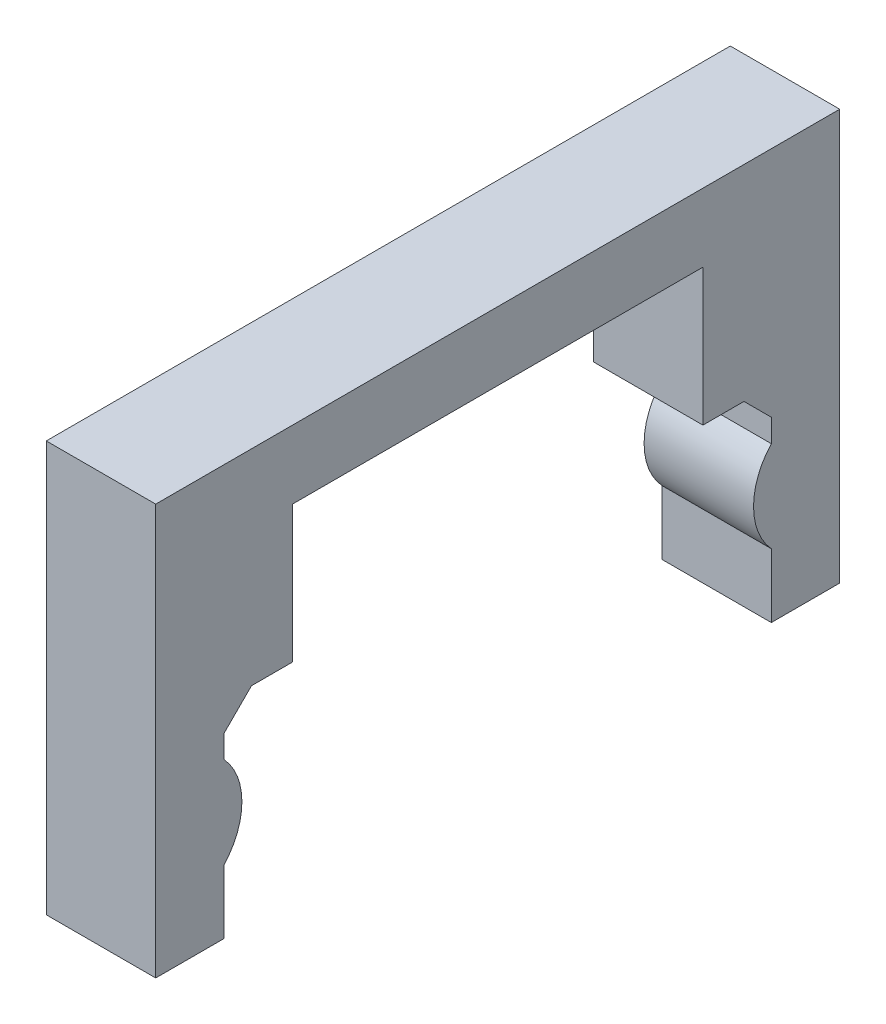
SolidWorks part; units mm, degrees
ref_plane "Front Plane" through (0, 0, 0) normal (0, 0, 1) x (1, 0, 0)
ref_plane "Top Plane" through (0, 0, 0) normal (0, 1, 0) x (1, 0, 0)
ref_plane "Right Plane" through (0, 0, 0) normal (1, 0, 0) x (0, 0, -1)
sketch "Sketch3" plane through (0, 0, 0) normal (1, 0, 0) x (0, 0, -1)
  line L0 (-101.8456, -9.1027) -> (-95.4956, -9.1027)
  line L1 (-95.4956, -9.1027) -> (-95.4956, 9.9473)
  line L2 (-95.4956, 9.9473) -> (-89.1456, 9.9473)
  line L3 (-89.1456, 9.9473) -> (-89.1456, 22.6473)
  line L4 (-89.1456, 22.6473) -> (-51.0456, 22.6473)
  line L5 (-51.0456, 22.6473) -> (-51.0456, 9.9473)
  line L6 (-51.0456, 9.9473) -> (-44.6956, 9.9473)
  line L7 (-44.6956, 9.9473) -> (-44.6956, -9.1027)
  line L8 (-44.6956, -9.1027) -> (-38.3456, -9.1027)
  line L9 (-38.3456, -9.1027) -> (-38.3456, 28.9973)
  line L10 (-38.3456, 28.9973) -> (-101.8456, 28.9973)
  line L11 (-101.8456, 28.9973) -> (-101.8456, -9.1027)
  dimension "D1" = 6.35
  dimension "D2" = 6.35
  dimension "D3" = 6.35
  dimension "D4" = 6.35
  dimension "D5" = 12.7
  dimension "D6" = 6.35
  dimension "D7" = 50.8
  dimension "D8" = 12.7
  dimension "D9" = 38.1
  dimension "D10" = 38.1
extrude "Boss-Extrude1" add sketch "Sketch3" along normal blind 10.16
sketch "Sketch4" plane through (10.16, 0, 0) normal (1, 0, 0) x (0, 0, -1)
  line L0 (-95.4956, 9.9473) -> (-89.1456, 9.9473) construction
  line L1 (-51.0456, 9.9473) -> (-44.6956, 9.9473) construction
  line L2 (-95.4956, -9.1027) -> (-95.4956, 9.9473) construction
  line L3 (-44.6956, 9.9473) -> (-44.6956, -9.1027) construction
  line L4 (-101.8456, -4.9062) -> (-101.8456, 7.0209)
  line L5 (-101.8456, 28.9973) -> (-101.8456, -9.1027) construction
  line L6 (-38.3456, -4.9062) -> (-38.3456, 7.0209)
  line L7 (-38.3456, -9.1027) -> (-38.3456, 28.9973) construction
  arc A0 (-101.8456, -4.9062) -> (-101.8456, 7.0209) centre (-100.0676, 1.0573) ccw
  arc A1 (-38.3456, 7.0209) -> (-38.3456, -4.9062) centre (-40.1236, 1.0573) ccw
  point P4 (-92.3206, 9.9473)
  dimension "D3" = 12.446
  dimension "D4" = 12.446
  dimension "D1" = 8.89
  dimension "D2" = 8.89
  dimension "D5" = 4.572
  dimension "D6" = 4.572
extrude "Boss-Extrude2" add sketch "Sketch4" against normal blind 10.16
chamfer "Chamfer1" distance 2.54 angle 45 2 edges at (5.08, 9.9473, 95.4956) (5.08, 9.9473, 44.6956)
